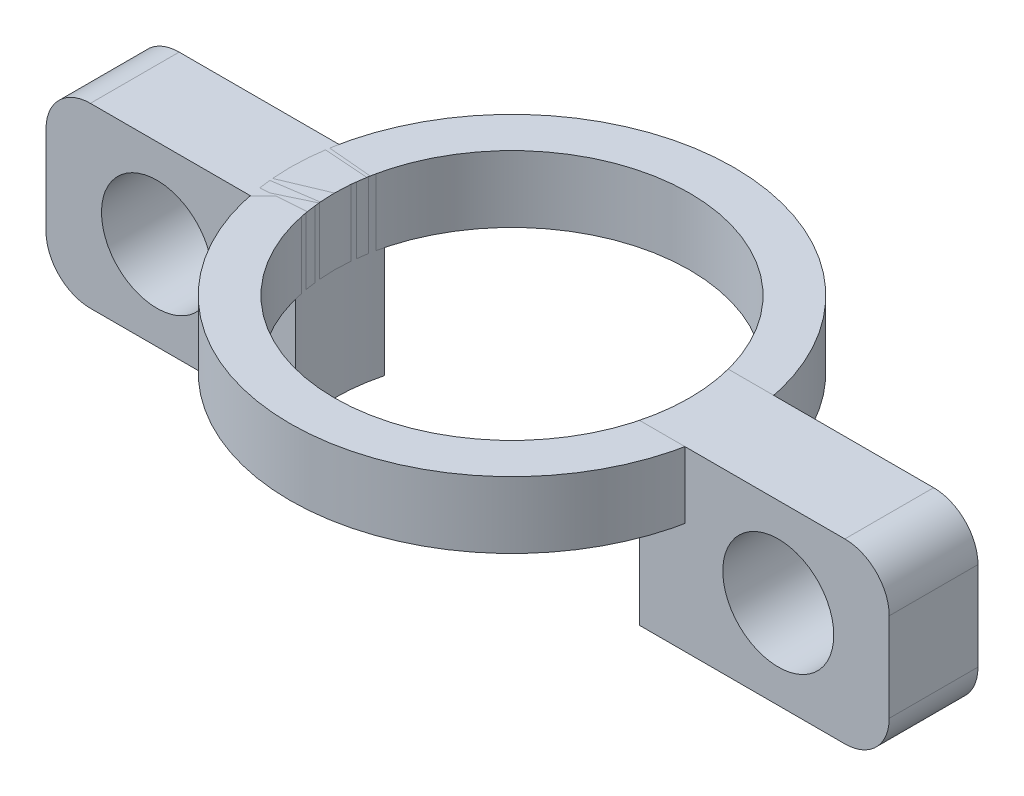
SolidWorks part; units mm, degrees
ref_plane "前视基准面" through (0, 0, 0) normal (0, 0, 1) x (1, 0, 0)
ref_plane "上视基准面" through (0, 0, 0) normal (0, 1, 0) x (1, 0, 0)
ref_plane "右视基准面" through (0, 0, 0) normal (1, 0, 0) x (0, 0, -1)
sketch "草图1" plane through (0, -55, 0) normal (0, -1, 0) x (-1, 0, 0)
  line L0 (0, 0) -> (8, 0) construction
  line L1 (7.746, 2) -> (19, 2)
  line L2 (19, 2) -> (19, -2)
  line L3 (19, -2) -> (7.746, -2)
  circle A0 centre (0, 0) radius 8 construction
  arc A1 (7.746, -2) -> (7.746, 2) centre (0, 0) ccw
  dimension "D1" = 4
  dimension "D2" = 11
extrude "凸台-拉伸1" add sketch "草图1" against normal blind 8
sketch "草图2" plane through (0, 0, -2) normal (0, 0, -1) x (-1, 0, 0)
  line L0 (19, -47) -> (19, -55) construction
  circle A0 centre (14, -51) radius 2.5
  point P5 (19, -51)
  dimension "D1" = 5
  dimension "D2" = 5
extrude "切除-拉伸1" cut sketch "草图2" against normal through all
fillet "圆角1" radius 2 2 edges at (-19, -55, 0) (-19, -47, 0)
pattern_circular "阵列(圆周)1" count 2 over 360 about axis through (0, 0, 0) along (0, 1, 0) of bodies 102
sketch "草图3" plane through (0, -47, 0) normal (0, 1, 0) x (1, 0, 0)
  circle A0 centre (0, 0) radius 8 construction
  circle A1 centre (0, 0) radius 8
extrude "拉伸-薄壁1" add sketch "草图3" against normal blind 3 separate body thin
